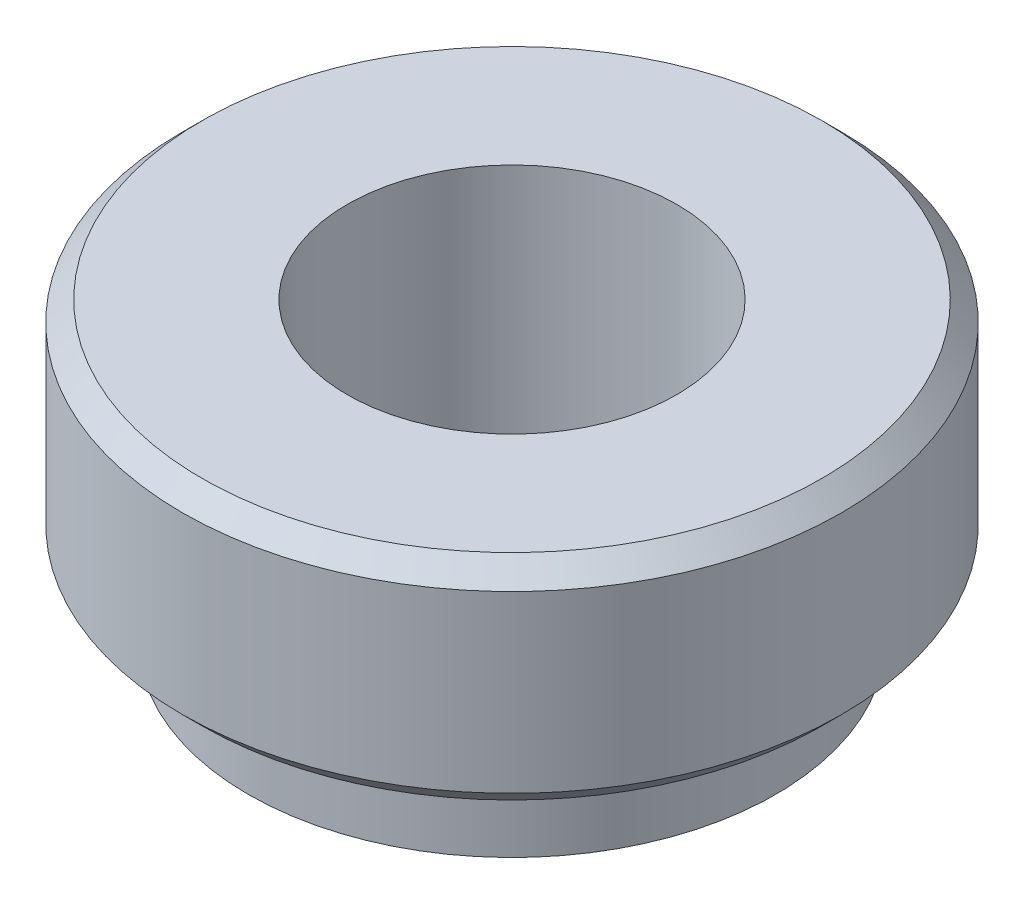
SolidWorks part; units mm, degrees
ref_plane "Plan de face" through (0, 0, 0) normal (0, 0, 1) x (1, 0, 0)
ref_plane "Plan de dessus" through (0, 0, 0) normal (0, 1, 0) x (1, 0, 0)
ref_plane "Plan de droite" through (0, 0, 0) normal (1, 0, 0) x (0, 0, -1)
sketch "Esquisse1" plane through (0, 0, 0) normal (0, 0, 1) x (1, 0, 0)
  line L0 (0, 0) -> (0, 7.1709) construction
  line L1 (-2.5, 0) -> (-2.5, 4.5)
  line L2 (-2.5, 4.5) -> (-5, 4.5)
  line L3 (-5, 4.5) -> (-5, 1.25)
  line L4 (-5, 1.25) -> (-4, 1.25)
  line L5 (-4, 1.25) -> (-4, 0)
  line L6 (-4, 0) -> (-2.5, 0)
  dimension "D1" = 10
  dimension "D2" = 8
  dimension "D3" = 5
  dimension "D4" = 3.25
  dimension "D5" = 4.5
revolve "Révolution1" add sketch "Esquisse1" angle 360 about L0
chamfer "Chanfrein1" distance 0.3 angle 45 2 edges at (0, 1.25, -5) (0, 4.5, -5)
